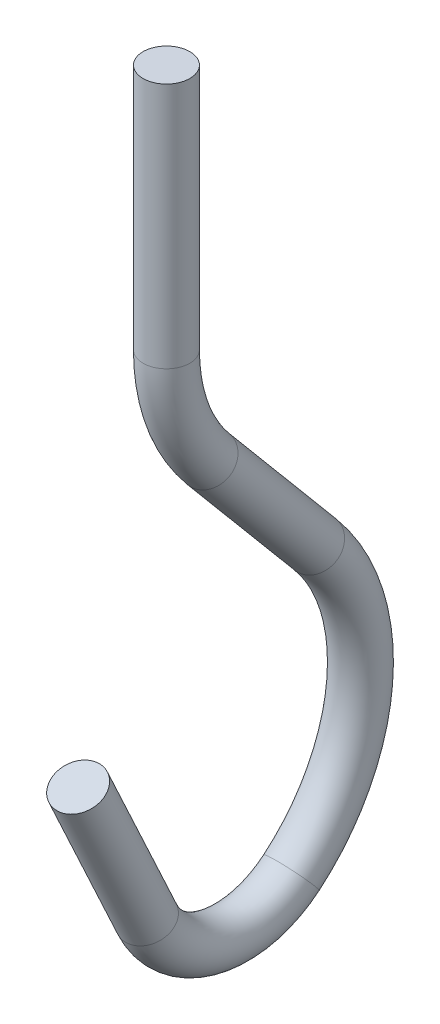
SolidWorks part; units mm, degrees
ref_plane "Front Plane" through (0, 0, 0) normal (0, 0, 1) x (1, 0, 0)
ref_plane "Top Plane" through (0, 0, 0) normal (0, 1, 0) x (1, 0, 0)
ref_plane "Right Plane" through (0, 0, 0) normal (1, 0, 0) x (0, 0, -1)
sketch "Sketch1" plane through (0, 0, 0) normal (1, 0, 0) x (0, 0, -1)
  line L0 (1.148, -9.8652) -> (4.0484, -13.3218)
  line L1 (-0.5307, -19.8573) -> (-2.404, -15.8163)
  arc A0 (0, -6.7111) -> (1.148, -9.8652) centre (4.907, -6.7111) ccw
  arc A1 (4.0484, -13.3218) -> (3.4, -20.7334) centre (0.0185, -16.7034) cw
  arc A2 (3.4, -20.7334) -> (-0.5307, -19.8573) centre (1.77, -18.7908) cw
  spline S0 degree 1 poles (0, 0) (0, -6.7111) knots 0 0 1 1
  point P9 (-0.5307, -19.8573)
sketch "Sketch2" plane through (0, 0, 0) normal (0, 1, 0) x (1, 0, 0)
  circle A0 centre (0, 0) radius 0.635
  dimension "D1" = 1.27
sweep "Sweep1" add profiles "Sketch2" path "Sketch1"
